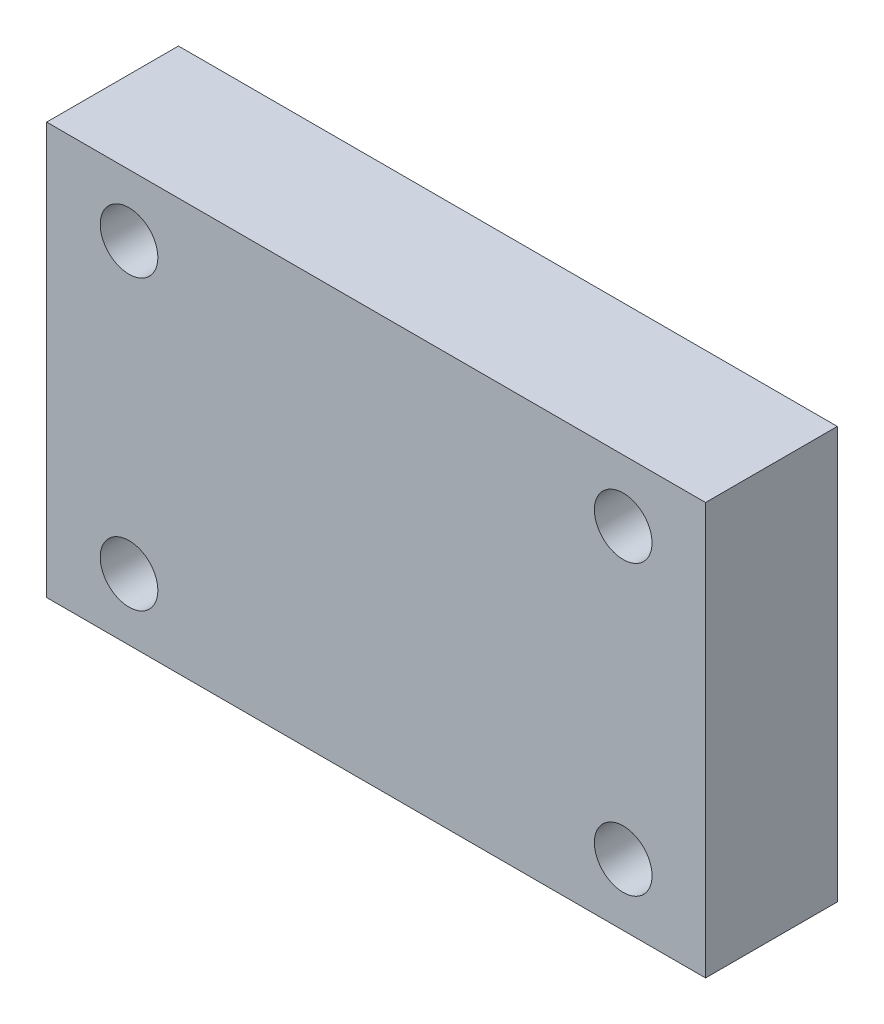
SolidWorks part; units mm, degrees
material "Caoutchouc naturel"
ref_plane "Plan de face" through (0, 0, 0) normal (0, 0, 1) x (1, 0, 0)
ref_plane "Plan de dessus" through (0, 0, 0) normal (0, 1, 0) x (1, 0, 0)
ref_plane "Plan de droite" through (0, 0, 0) normal (1, 0, 0) x (0, 0, -1)
sketch "Esquisse1" plane through (0, 0, 0) normal (0, 0, 1) x (1, 0, 0)
  line L1 (-40, -25) -> (40, -25)
  line L2 (-40, -25) -> (-40, 25)
  line L3 (-40, 25) -> (40, 25)
  line L4 (40, -25) -> (40, 25)
  line L5 (-40, -25) -> (40, 25) construction
  line L6 (-40, 25) -> (40, -25) construction
  point P0 (0, 0)
  dimension "D1" = 50
  dimension "D2" = 80
extrude "Boss.-Extru.1" add sketch "Esquisse1" along normal mid plane 16
sketch "Esquisse2" plane through (0, 0, 8) normal (0, 0, 1) x (1, 0, 0)
  line L0 (0, 0) -> (0, 39.6057) construction
  line L1 (40, 25) -> (-40, 25) construction
  line L3 (30, -17.5) -> (-30, -17.5) construction
  line L4 (30, -17.5) -> (30, 17.5) construction
  line L5 (30, 17.5) -> (-30, 17.5) construction
  line L6 (-30, -17.5) -> (-30, 17.5) construction
  line L7 (30, -17.5) -> (-30, 17.5) construction
  line L8 (30, 17.5) -> (-30, -17.5) construction
  circle A0 centre (-30, 17.5) radius 3.5
  circle A1 centre (30, 17.5) radius 3.5
  circle A2 centre (-30, -17.5) radius 3.5
  circle A3 centre (30, -17.5) radius 3.5
  dimension "D1" = 7
  dimension "D2" = 60
  dimension "D3" = 7.5
extrude "Enlèv. mat.-Extru.1" cut sketch "Esquisse2" against normal through all
